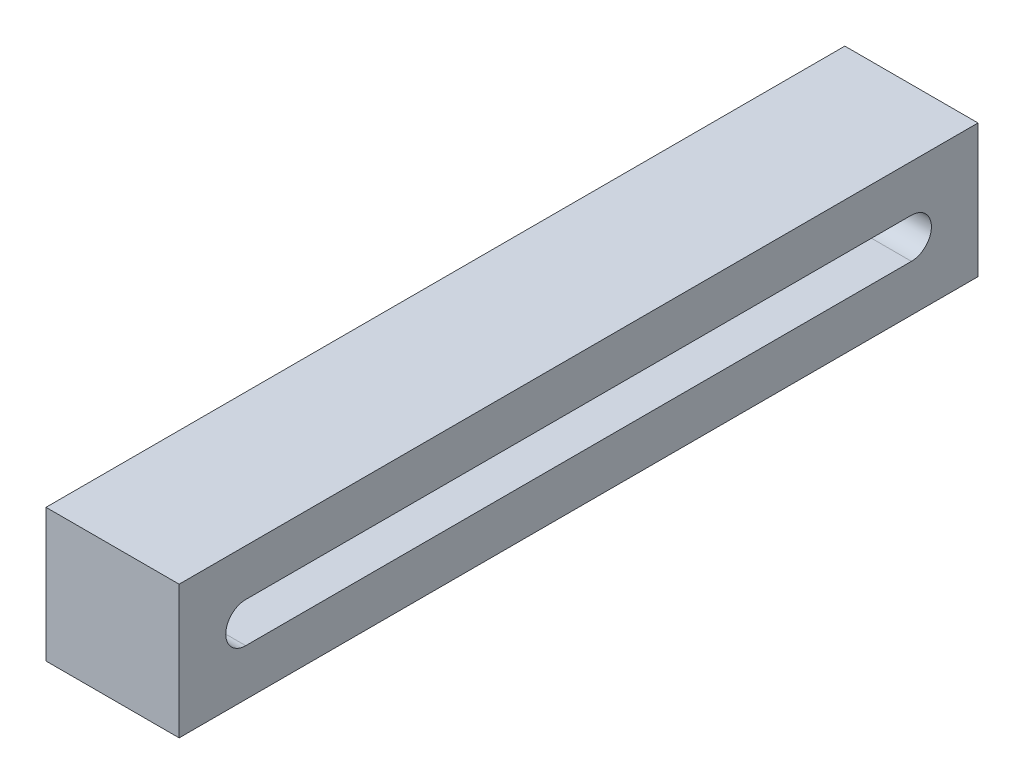
SolidWorks part; units mm, degrees
ref_plane "前视基准面" through (0, 0, 0) normal (0, 0, 1) x (1, 0, 0)
ref_plane "上视基准面" through (0, 0, 0) normal (0, 1, 0) x (1, 0, 0)
ref_plane "右视基准面" through (0, 0, 0) normal (1, 0, 0) x (0, 0, -1)
sketch "草图1" plane through (0, 0, 0) normal (1, 0, 0) x (0, 0, -1)
  line L0 (3.434, 6.122) -> (53.434, 6.122)
  line L1 (-1.566, 9.622) -> (58.434, 9.622)
  line L2 (-1.566, 9.622) -> (-1.566, -0.378)
  line L3 (-1.566, -0.378) -> (58.434, -0.378)
  line L4 (58.434, 9.622) -> (58.434, -0.378)
  line L6 (3.434, 3.122) -> (53.434, 3.122)
  arc A0 (3.434, 3.122) -> (3.434, 6.122) centre (3.434, 4.622) cw
  arc A1 (53.434, 6.122) -> (53.434, 3.122) centre (53.434, 4.622) cw
  dimension "D1" = 10
  dimension "D2" = 60
  dimension "D3" = 3
  dimension "D4" = 3.5
  dimension "D5" = 50
  dimension "D6" = 5
  dimension "D7" = 50
  dimension "D8" = 5
extrude "凸台-拉伸1" add sketch "草图1" along normal blind 10
